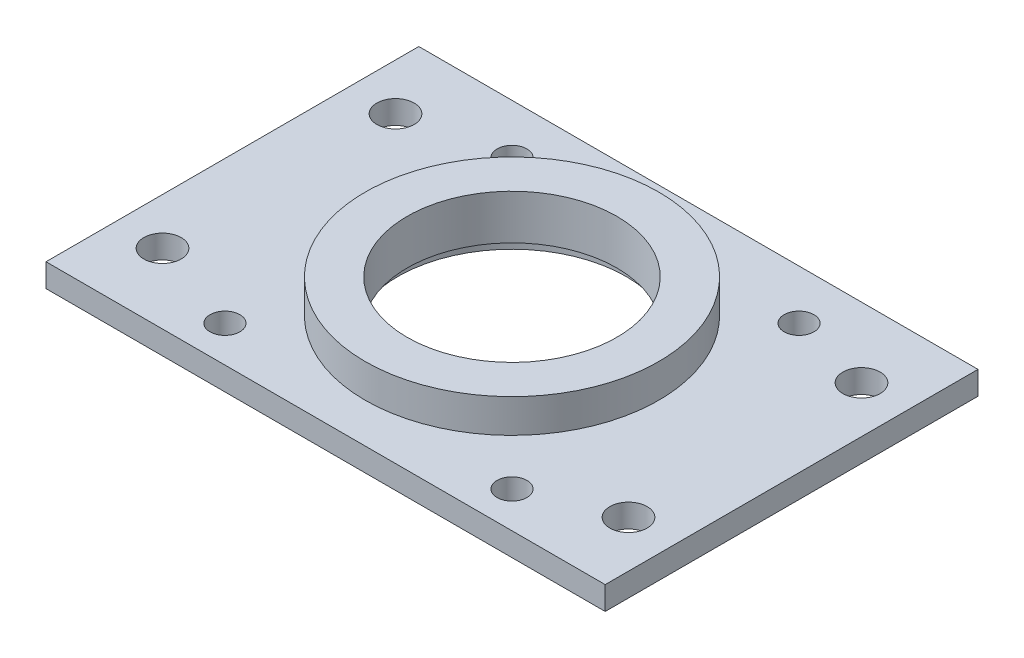
SolidWorks part; units mm, degrees
ref_plane "Front Plane" through (0, 0, 0) normal (0, 0, 1) x (1, 0, 0)
ref_plane "Top Plane" through (0, 0, 0) normal (0, 1, 0) x (1, 0, 0)
ref_plane "Right Plane" through (0, 0, 0) normal (1, 0, 0) x (0, 0, -1)
sketch "Sketch1" plane through (0, 0, 0) normal (0, 1, 0) x (1, 0, 0)
  circle A0 centre (0, 0) radius 20.0025
  circle A1 centre (0, 0) radius 14.2875
  point P0 (0, 0)
  dimension "D1" = 40.005
  dimension "D2" = 28.575
extrude "Boss-Extrude1" add sketch "Sketch1" along normal blind 4.572
sketch "Sketch2" plane through (0, 0, 0) normal (0, -1, 0) x (1, 0, 0)
  line L1 (38.1, -25.4) -> (-38.1, -25.4)
  line L2 (38.1, -25.4) -> (38.1, 25.4)
  line L3 (38.1, 25.4) -> (-38.1, 25.4)
  line L4 (-38.1, -25.4) -> (-38.1, 25.4)
  line L5 (38.1, -25.4) -> (-38.1, 25.4) construction
  line L6 (38.1, 25.4) -> (-38.1, -25.4) construction
  circle A0 centre (0, 0) radius 14.2875
  point P0 (0, 0)
  dimension "D1" = 50.8
  dimension "D2" = 76.2
extrude "Boss-Extrude2" add sketch "Sketch2" along normal blind 3.175
sketch "Sketch3" plane through (0, -3.175, 0) normal (0, -1, 0) x (1, 0, 0)
  circle A0 centre (0, 0) radius 15.5575
  dimension "D1" = 31.115
extrude "Cut-Extrude1" cut sketch "Sketch3" against normal blind 1.651
sketch "Sketch5" plane through (0, 0, 0) normal (0, 1, 0) x (1, 0, 0)
  line L1 (-18.65, 18.65) -> (18.6499, 18.65) construction
  line L2 (-18.65, 18.65) -> (-18.65, -18.65) construction
  line L3 (-18.65, -18.65) -> (18.65, -18.65) construction
  line L4 (18.6499, 18.65) -> (18.65, -18.65) construction
  line L5 (18.6499, 18.65) -> (-18.65, -18.65) construction
  line L6 (31.75, -15.875) -> (-31.75, -15.875) construction
  line L7 (31.75, -15.875) -> (31.75, 15.875) construction
  line L8 (31.75, 15.875) -> (-31.75, 15.875) construction
  line L9 (-31.75, -15.875) -> (-31.75, 15.875) construction
  line L10 (31.75, -15.875) -> (-31.75, 15.875) construction
  line L11 (31.75, 15.875) -> (-31.75, -15.875) construction
  circle A0 centre (-18.65, 18.65) radius 2.032
  circle A1 centre (20.466, 18.65) radius 2.032
  circle A2 centre (-18.6499, -20.466) radius 2.032
  circle A3 centre (20.4661, -20.466) radius 2.032
  circle A4 centre (-31.75, 15.875) radius 2.54
  circle A5 centre (31.75, 15.875) radius 2.54
  circle A6 centre (31.75, -15.875) radius 2.54
  circle A7 centre (-31.75, -15.875) radius 2.54
  point P4 (0, 0)
  point P8 (0, 0)
  dimension "D2" = 4.064
  dimension "D7" = 5.08
  dimension "D1" = 37.2999
  dimension "D5" = 63.5
  dimension "D6" = 31.75
  dimension "D3" = 2
  dimension "D4" = 2
  dimension "D8" = 2
  dimension "D9" = 2
extrude "Cut-Extrude2" cut sketch "Sketch5" against normal through all
